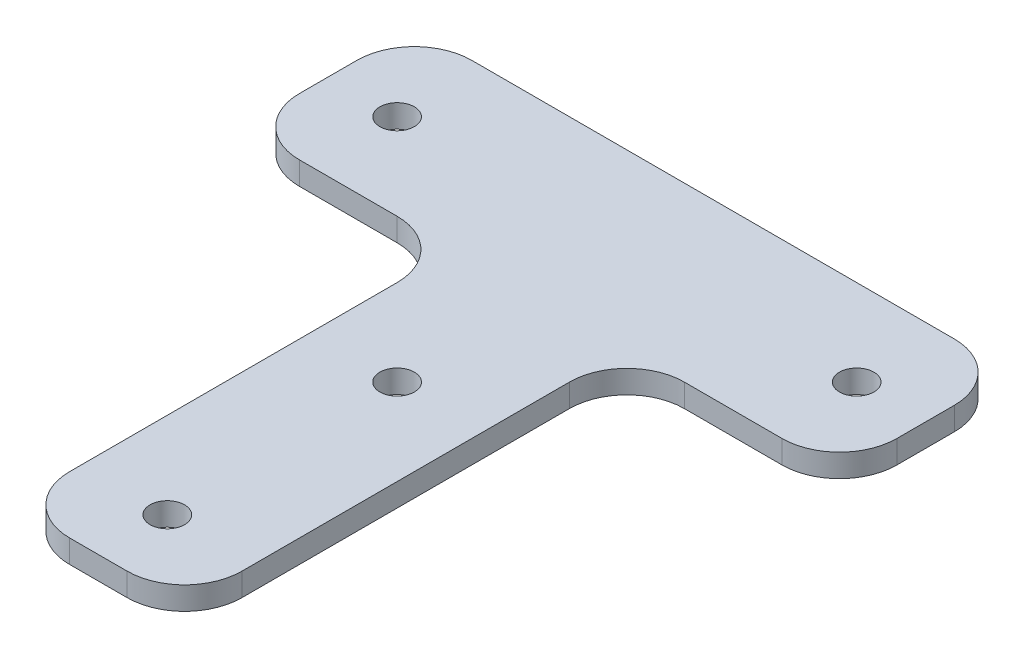
SolidWorks part; units mm, degrees
material "Thornel Mat VMA"
ref_plane "Front Plane" through (0, 0, 0) normal (0, 0, 1) x (1, 0, 0)
ref_plane "Top Plane" through (0, 0, 0) normal (0, 1, 0) x (1, 0, 0)
ref_plane "Right Plane" through (0, 0, 0) normal (1, 0, 0) x (0, 0, -1)
sketch "Sketch1" plane through (0, 0, 0) normal (0, 1, 0) x (1, 0, 0)
  line L0 (0, 0) -> (0, -40) construction
  line L1 (0, 0) -> (20, 0) construction
  line L2 (7.5, -46) -> (7.5, -7.5)
  line L3 (7.5, -7.5) -> (26, -7.5)
  line L4 (26, -7.5) -> (26, 7.5)
  line L5 (-7.5, -46) -> (-7.5, -7.5)
  line L6 (-26, -7.5) -> (-26, 7.5)
  line L7 (-7.5, -7.5) -> (-26, -7.5)
  line L8 (7.5, -46) -> (-7.5, -46)
  line L9 (26, 7.5) -> (-26, 7.5)
  circle A0 centre (0, -40) radius 1.5
  circle A1 centre (0, -20) radius 1.5
  circle A2 centre (20, 0) radius 1.5
  circle A3 centre (-20, 0) radius 1.5
  circle A4 centre (0, 0) radius 1.5 construction
  dimension "D1" = 3
  dimension "D2" = 40
  dimension "D3" = 20
  dimension "D4" = 20
  dimension "D5" = 15
  dimension "D6" = 6
  dimension "D7" = 6
extrude "Boss-Extrude1" add sketch "Sketch1" along normal blind 2
fillet "Fillet1" radius 5 8 edges at (-26, 1, 7.5) (-26, 1, -7.5) (26, 1, -7.5) (26, 1, 7.5) (7.5, 1, 46) (-7.5, 1, 46) (-7.5, 1, 7.5) (7.5, 1, 7.5)
